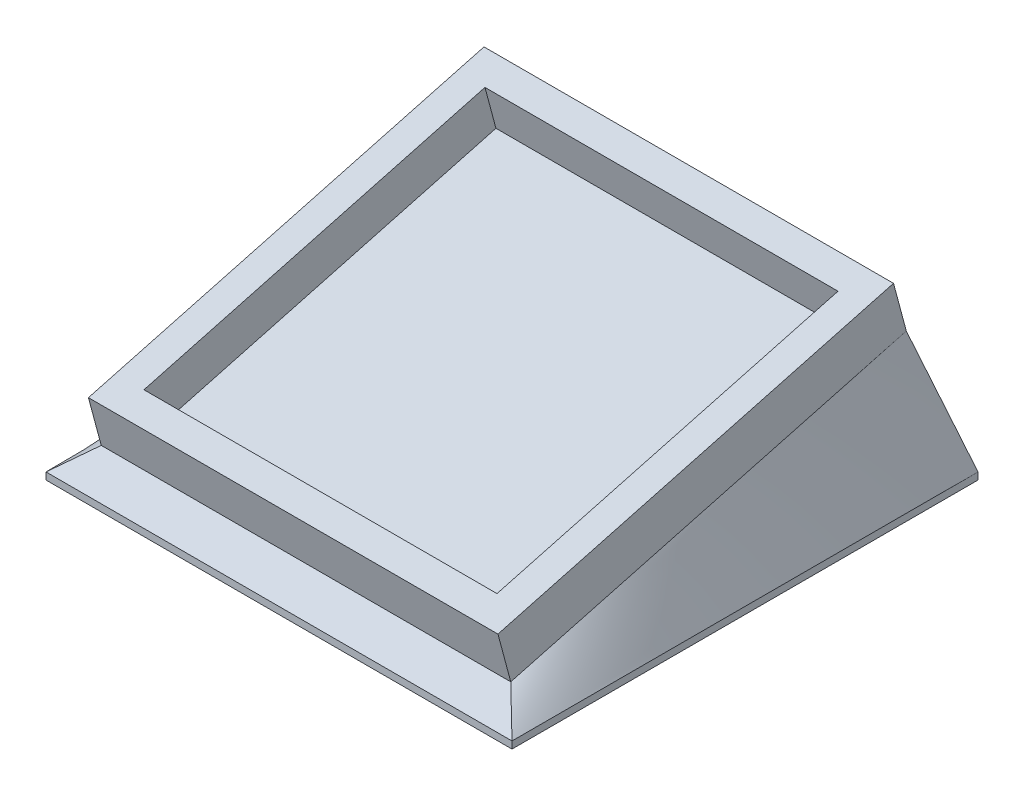
SolidWorks part; units mm, degrees
ref_plane "Front Plane" through (0, 0, 0) normal (0, 0, 1) x (1, 0, 0)
ref_plane "Top Plane" through (0, 0, 0) normal (0, 1, 0) x (1, 0, 0)
ref_plane "Right Plane" through (0, 0, 0) normal (1, 0, 0) x (0, 0, -1)
sketch "Sketch1" plane through (0, 0, 0) normal (0, 1, 0) x (1, 0, 0)
  line L1 (-22.2888, 13.0013) -> (14.5412, 13.0013)
  line L2 (-22.2888, 13.0013) -> (-22.2888, -23.8287)
  line L3 (-22.2888, -23.8287) -> (14.5412, -23.8287)
  line L4 (14.5412, 13.0013) -> (14.5412, -23.8287)
  dimension "D1" = 36.83
  dimension "D2" = 36.83
extrude "Boss-Extrude1" add sketch "Sketch1" along normal blind 0.635
sketch "Sketch2" plane through (0, 0.635, 0) normal (0, 1, 0) x (1, 0, 0)
  line L0 (14.5412, 13.0013) -> (-22.2888, 13.0013) construction
  line L1 (-19.7488, 10.4613) -> (12.0012, 10.4613)
  line L2 (-19.7488, 10.4613) -> (-19.7488, -21.2887)
  line L3 (-19.7488, -21.2887) -> (12.0012, -21.2887)
  line L4 (12.0012, 10.4613) -> (12.0012, -21.2887)
  line L5 (-22.2888, 13.0013) -> (-22.2888, -23.8287) construction
  line L7 (-22.2888, 13.0013) -> (14.5412, 13.0013)
  line L8 (-22.2888, 13.0013) -> (-22.2888, -23.8287)
  line L9 (-22.2888, -23.8287) -> (14.5412, -23.8287)
  line L10 (14.5412, 13.0013) -> (14.5412, -23.8287)
  dimension "D1" = 31.75
  dimension "D2" = 31.75
  dimension "D3" = 2.54
  dimension "D4" = 2.54
extrude "Boss-Extrude2" add sketch "Sketch2" along normal blind 3.81 contours L8 L7 L10 L9 | L2 L1 L4 L3
move or copy body "Body-Move/Copy1" bodies to move or copy 102 copy no translate (0, 7.62, 0)
sketch "Sketch3" plane through (0, 0, 0) normal (0, 1, 0) x (1, 0, 0)
  line L0 (-22.2888, 13.0013) -> (-22.2888, -23.8287) construction
  line L1 (-24.8288, 15.5413) -> (17.0812, 15.5413)
  line L2 (-24.8288, 15.5413) -> (-24.8288, -26.3687)
  line L3 (-24.8288, -26.3687) -> (17.0812, -26.3687)
  line L4 (17.0812, 15.5413) -> (17.0812, -26.3687)
  line L5 (-22.2888, -23.8287) -> (14.5412, -23.8287) construction
  dimension "D1" = 41.91
  dimension "D2" = 41.91
  dimension "D3" = 2.54
  dimension "D4" = 2.54
extrude "Boss-Extrude3" add sketch "Sketch3" along normal blind 0.635 separate body
move or copy body "Body-Move/Copy2" bodies to move or copy 103 copy no rotation origin (0, 4.7625, 5.4137) rotation axis (1, 0, 0) rotation angle 15
loft "Loft1" add section face at (-3.8738, 7.5226, 6.1533) section face at (-3.8738, 0.635, 5.4137)
sketch "Sketch4" plane through (0, 4.7481, -14.1623) normal (0, 0.3179, -0.9481) x (-1, 0, 0)
  line L0 (-10.8328, 0.7419) -> (18.3772, 0.7419) construction
  line L1 (-17.0812, -4.3381) -> (24.8288, -4.3381) construction
  text T0 "15 x 0"
  dimension "D1" = 29.21
  dimension "D2" = 5.08
extrude "Cut-Extrude1" cut sketch "Sketch4" against normal blind 0.635
